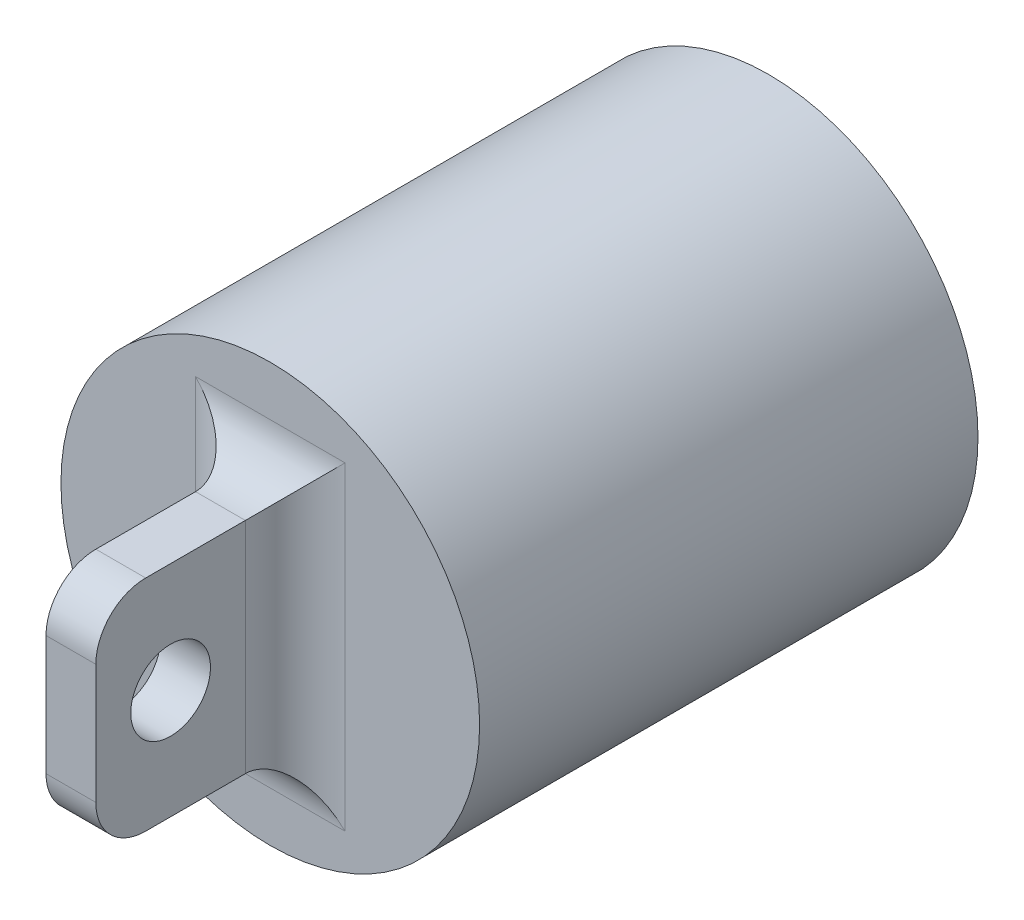
SolidWorks part; units mm, degrees
material "AISI 1020"
ref_plane "Front Plane" through (0, 0, 0) normal (0, 0, 1) x (1, 0, 0)
ref_plane "Top Plane" through (0, 0, 0) normal (0, 1, 0) x (1, 0, 0)
ref_plane "Right Plane" through (0, 0, 0) normal (1, 0, 0) x (0, 0, -1)
sketch "Sketch1" plane through (0, 0, 0) normal (0, 0, 1) x (1, 0, 0)
  circle A0 centre (0, 0) radius 21
  dimension "D1" = 42
extrude "Boss-Extrude1" add sketch "Sketch1" along normal blind 50
sketch "Sketch2" plane through (0, 0, 0) normal (1, 0, 0) x (0, 0, -1)
  line L0 (-50, 21) -> (-50, -21) construction
  line L1 (-50, 11) -> (-70, 11)
  line L2 (-50, 11) -> (-50, -11)
  line L3 (-50, -11) -> (-70, -11)
  line L4 (-70, 11) -> (-70, -11)
  dimension "D1" = 10
  dimension "D2" = 10
  dimension "D3" = 20
extrude "Boss-Extrude2" add sketch "Sketch2" along normal mid plane 5
fillet "Fillet1" radius 5 4 edges at (0, -11, 50) (2.5, 0, 50) (0, 11, 50) (-2.5, 0, 50)
fillet "Fillet2" radius 5 2 edges at (0, 11, 70) (0, -11, 70)
sketch "Sketch3" plane through (2.5, 0, 0) normal (1, 0, 0) x (0, 0, -1)
  line L0 (-62.5, 0) -> (-70, 0) construction
  line L1 (-70, 6) -> (-70, -6) construction
  line L2 (-62.5, 0) -> (-55, 0) construction
  line L3 (-55, -11) -> (-55, 11) construction
  circle A0 centre (-62.5, 0) radius 4
  dimension "D1" = 8
extrude "Cut-Extrude1" cut sketch "Sketch3" against normal through all
equation "\"D2@Sketch2\"=\"D1@Sketch2\""
